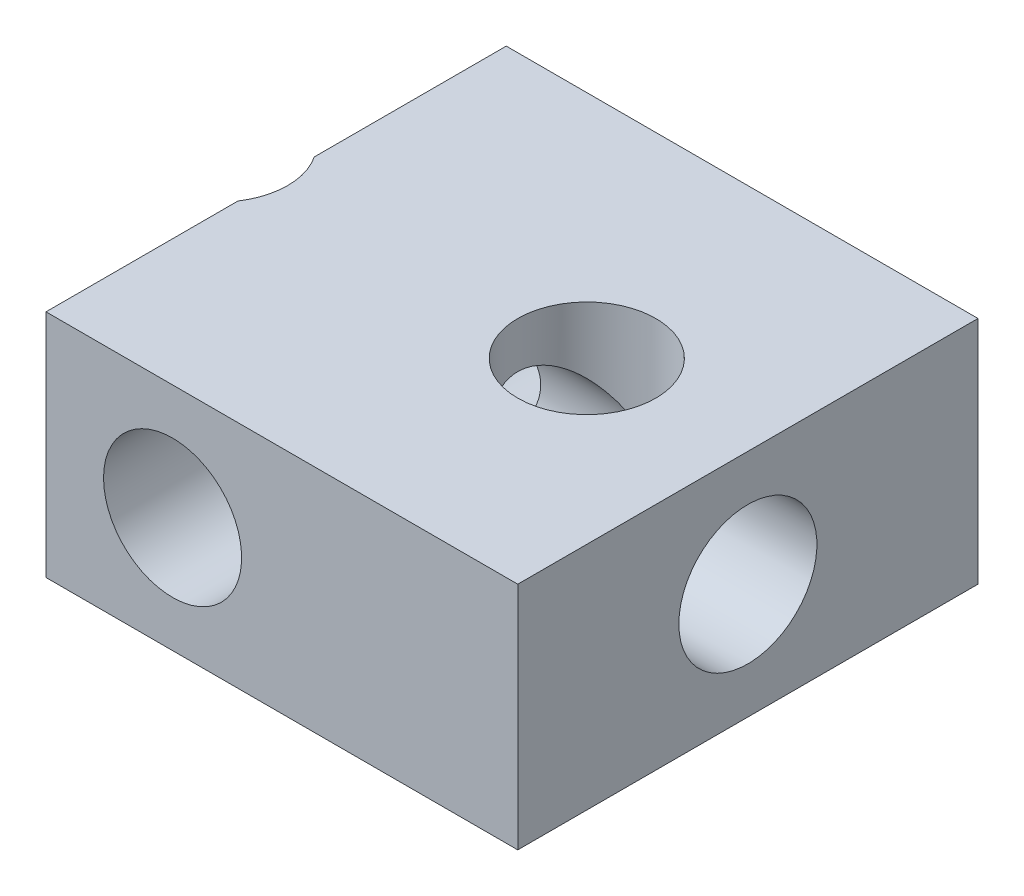
SolidWorks part; units mm, degrees
ref_plane "Front Plane" through (0, 0, 0) normal (0, 0, 1) x (1, 0, 0)
ref_plane "Top Plane" through (0, 0, 0) normal (0, 1, 0) x (1, 0, 0)
ref_plane "Right Plane" through (0, 0, 0) normal (1, 0, 0) x (0, 0, -1)
sketch "Sketch1" plane through (0, 0, 0) normal (0, 1, 0) x (1, 0, 0)
  line L0 (-4, 0) -> (4, 0) construction
  line L1 (7.5, -5) -> (-7.5, -5)
  line L2 (7.5, -5) -> (7.5, 5)
  line L3 (7.5, 5) -> (-7.5, 5)
  line L4 (-7.5, -5) -> (-7.5, 5)
  line L5 (7.5, -5) -> (-7.5, 5) construction
  line L6 (7.5, 5) -> (-7.5, -5) construction
  circle A0 centre (4, 0) radius 1.5
  circle A1 centre (-4, 0) radius 1.5
  point P0 (0, 0)
  dimension "D4" = 3
  dimension "D1" = 15
  dimension "D2" = 10
  dimension "D3" = 8
extrude "Boss-Extrude1" add sketch "Sketch1" along normal blind 5
sketch "Sketch2" plane through (-7.5, 0, 0) normal (-1, 0, 0) x (0, 0, 1)
  line L0 (0, 0) -> (0, 5) construction
  line L1 (-5, 5) -> (5, 5) construction
  circle A0 centre (0, 2.5) radius 1.5
  dimension "D1" = 3
extrude "Cut-Extrude1" cut sketch "Sketch2" against normal through all both and the other way through all
sketch "Sketch3" plane through (0, 0, -5) normal (0, 0, -1) x (-1, 0, 0)
  line L0 (0, 0) -> (0, 5) construction
  line L1 (-7.5, 5) -> (7.5, 5) construction
  circle A0 centre (0, 2.5) radius 1.5
  dimension "D1" = 3
extrude "Cut-Extrude2" cut sketch "Sketch3" against normal through all both and the other way through all
sketch "Sketch4" plane through (-7.5, 0, 0) normal (-1, 0, 0) x (0, 0, 1)
  line L4 (-5, 0) -> (5, 0)
  line L5 (5, 0) -> (5, 5)
  line L6 (5, 5) -> (-5, 5)
  line L7 (-5, 5) -> (-5, 0)
  line L8 (-5, 0) -> (5, 0)
  line L9 (5, 0) -> (5, 5)
  line L10 (5, 5) -> (-5, 5)
  line L11 (-5, 5) -> (-5, 0)
  dimension "D1" = 0
extrude "Cut-Extrude3" cut sketch "Sketch4" against normal blind 4.75
